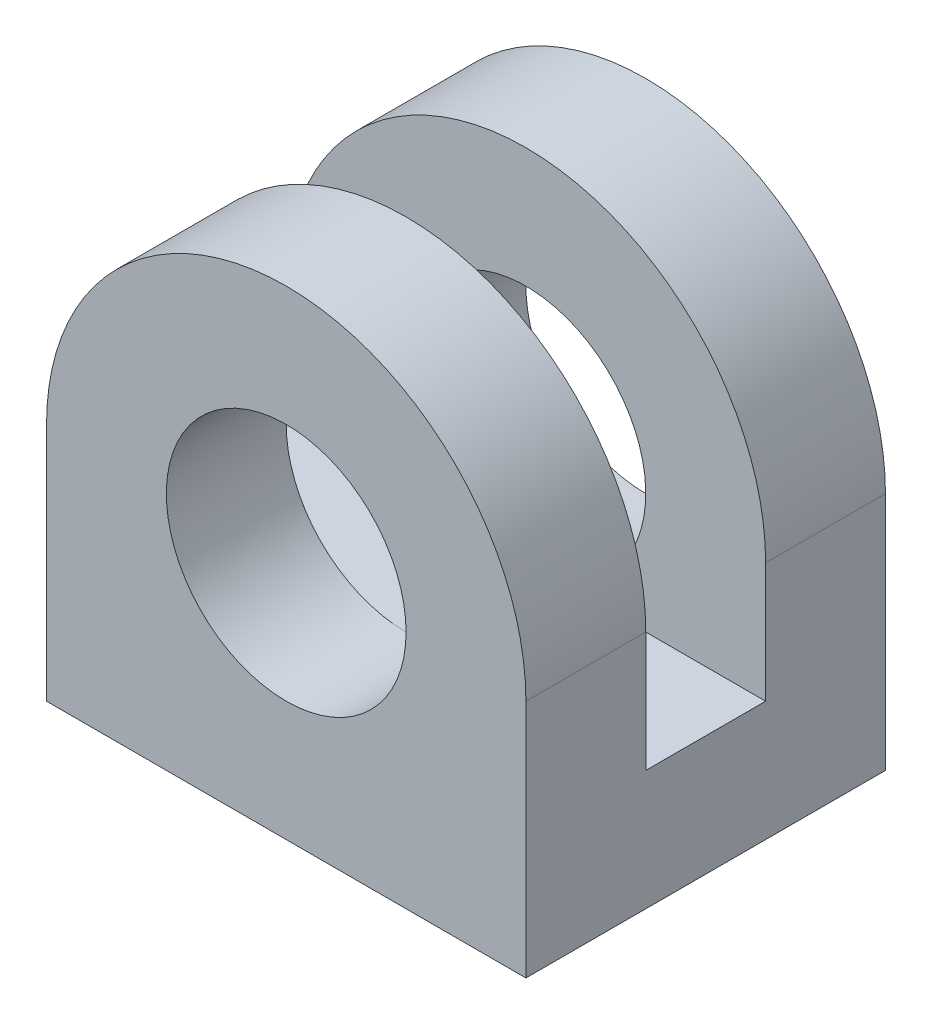
SolidWorks part; units mm, degrees
material "AISI 1020"
ref_plane "Plano frontal" through (0, 0, 0) normal (0, 0, 1) x (1, 0, 0)
ref_plane "Plano superior" through (0, 0, 0) normal (0, 1, 0) x (1, 0, 0)
ref_plane "Plano direito" through (0, 0, 0) normal (1, 0, 0) x (0, 0, -1)
sketch "Esboço1" plane through (0, 0, 0) normal (0, 0, 1) x (1, 0, 0)
  line L0 (-20, 0) -> (20, 0)
  line L1 (20, 0) -> (20, 20)
  line L2 (-20, 20) -> (-20, 0)
  arc A0 (20, 20) -> (-20, 20) centre (0, 20) ccw
  circle A1 centre (0, 20) radius 10
  point P6 (0, 0)
  dimension "D2" = 20
  dimension "D1" = 20
  dimension "D3" = 40
extrude "Ressalto-extrusão1" add sketch "Esboço1" along normal mid plane 30
sketch "Esboço2" plane through (20, 0, 0) normal (1, 0, 0) x (0, 0, -1)
  line L0 (-5, 46.6813) -> (-5, 10)
  line L1 (-5, 10) -> (5, 10)
  line L2 (5, 10) -> (5, 46.6813)
  line L3 (5, 46.6813) -> (-5, 46.6813)
  line L4 (0, 0) -> (0, 10) construction
  line L5 (-15, 0) -> (15, 0) construction
  dimension "D1" = 10
  dimension "D2" = 10
extrude "Corte-extrusão1" cut sketch "Esboço2" against normal through all
